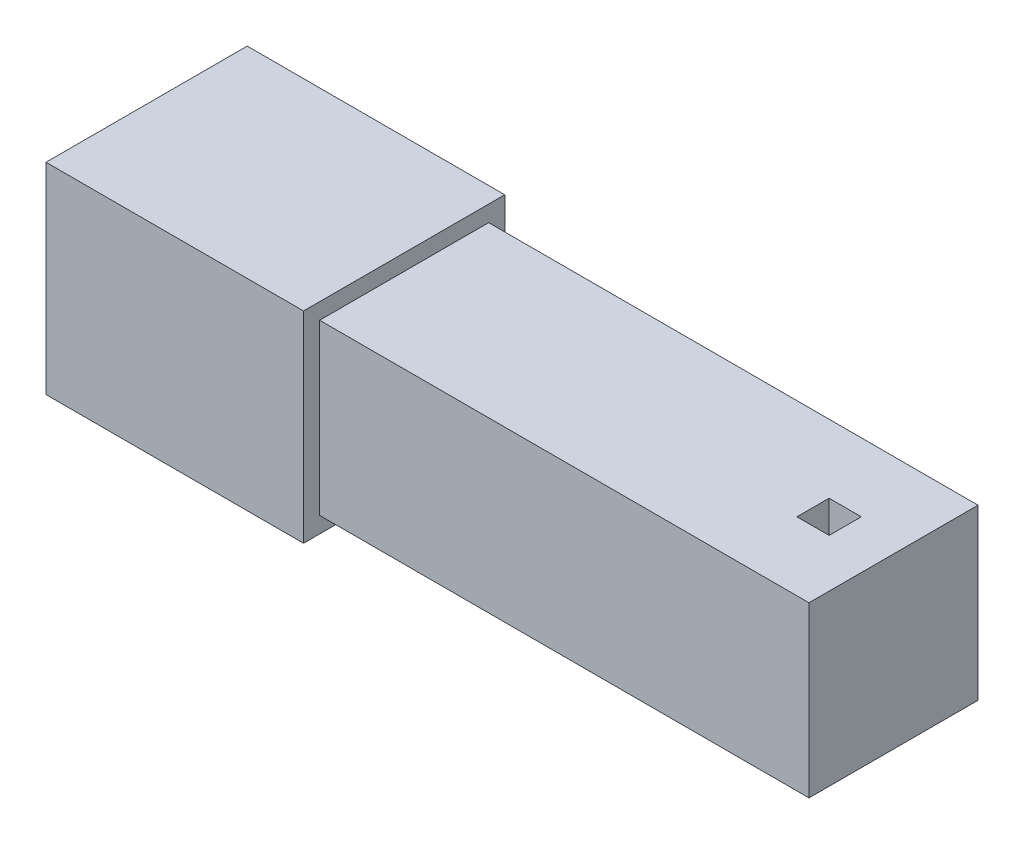
SolidWorks part; units mm, degrees
ref_plane "Front Plane" through (0, 0, 0) normal (0, 0, 1) x (1, 0, 0)
ref_plane "Top Plane" through (0, 0, 0) normal (0, 1, 0) x (1, 0, 0)
ref_plane "Right Plane" through (0, 0, 0) normal (1, 0, 0) x (0, 0, -1)
sketch "Sketch1" plane through (0, 0, 0) normal (1, 0, 0) x (0, 0, -1)
  line L1 (-52.5, 52.5) -> (52.5, 52.5)
  line L2 (-52.5, 52.5) -> (-52.5, -52.5)
  line L3 (-52.5, -52.5) -> (52.5, -52.5)
  line L4 (52.5, 52.5) -> (52.5, -52.5)
  line L5 (-52.5, 52.5) -> (52.5, -52.5) construction
  line L6 (-52.5, -52.5) -> (52.5, 52.5) construction
  point P0 (0, 0)
  dimension "D1" = 105
extrude "Boss-Extrude1" add sketch "Sketch1" along normal blind 304 contours L2 L3 L4 L1
sketch "Sketch2" plane through (0, 0, 0) normal (-1, 0, 0) x (0, 0, 1)
  line L1 (-10, 10) -> (10, 10)
  line L2 (-10, 10) -> (-10, -10)
  line L3 (-10, -10) -> (10, -10)
  line L4 (10, 10) -> (10, -10)
  line L5 (-10, 10) -> (10, -10) construction
  line L6 (-10, -10) -> (10, 10) construction
  point P0 (0, 0)
  dimension "D1" = 20
extrude "Boss-Extrude2" add sketch "Sketch2" along normal blind 152
sketch "Sketch3" plane through (0, 0, 0) normal (-1, 0, 0) x (0, 0, 1)
  line L1 (-52.5, -52.5) -> (52.5, -52.5)
  line L2 (-52.5, -52.5) -> (-52.5, 52.5)
  line L3 (-52.5, 52.5) -> (52.5, 52.5)
  line L4 (52.5, -52.5) -> (52.5, 52.5)
  line L5 (-52.5, -52.5) -> (52.5, 52.5) construction
  line L6 (-52.5, 52.5) -> (52.5, -52.5) construction
  point P0 (0, 0)
extrude "Extrude-Thin1" add sketch "Sketch3" along normal blind 160 separate body thin
sketch "Sketch4" plane through (0, -52.5, 0) normal (0, -1, 0) x (1, 0, 0)
  line L0 (304, 0) -> (0, 0) construction
  line L1 (304, 52.5) -> (304, -52.5) construction
  line L3 (254, 10) -> (274, 10)
  line L4 (254, 10) -> (254, -10)
  line L5 (254, -10) -> (274, -10)
  line L6 (274, 10) -> (274, -10)
  line L7 (254, 10) -> (274, -10) construction
  line L8 (254, -10) -> (274, 10) construction
  point P5 (264, 0)
  dimension "D1" = 20
  dimension "D2" = 40
extrude "Cut-Extrude1" cut sketch "Sketch4" against normal blind 160
